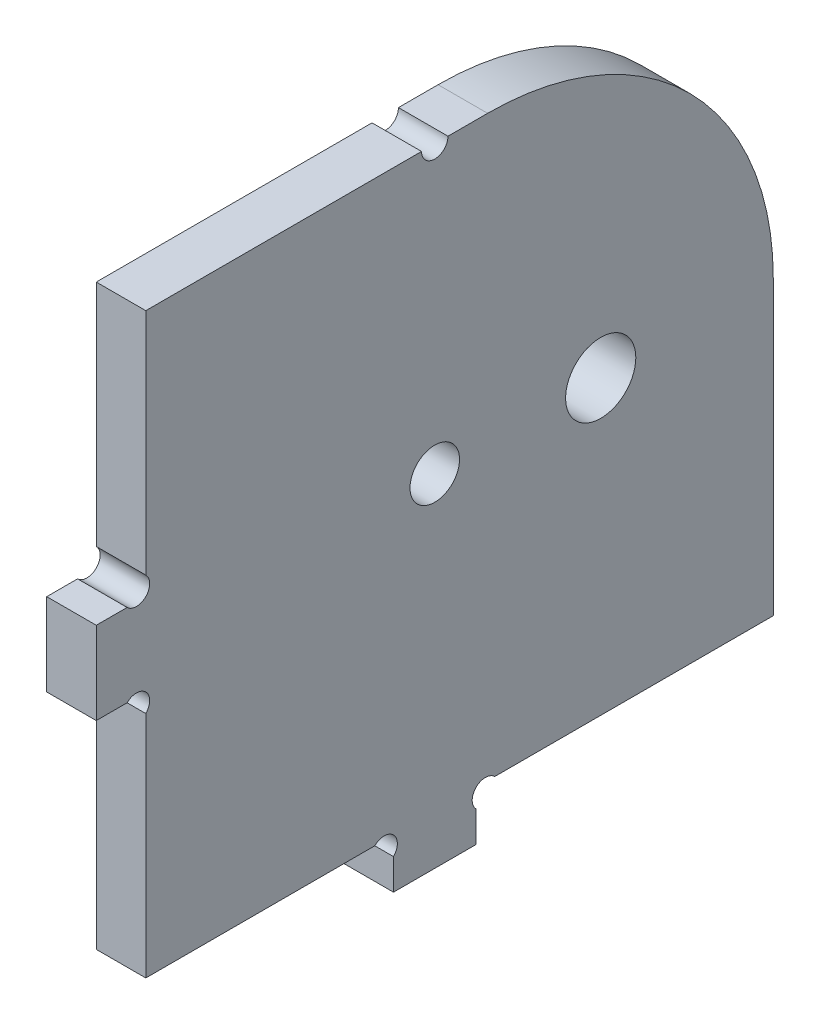
SolidWorks part; units mm, degrees
ref_plane "Plan de face" through (0, 0, 0) normal (0, 0, 1) x (1, 0, 0)
ref_plane "Plan de dessus" through (0, 0, 0) normal (0, 1, 0) x (1, 0, 0)
ref_plane "Plan de droite" through (0, 0, 0) normal (1, 0, 0) x (0, 0, -1)
sketch "Esquisse1" plane through (0, 0, 0) normal (1, 0, 0) x (0, 0, -1)
  line L0 (0, -4.5625) -> (0, 134.1836) construction
  line L1 (-32.3115, 0) -> (104.4265, 0) construction
  line L2 (-24.3695, 6) -> (94.833, 6) construction
  line L3 (6, -26.2376) -> (6, 112.02) construction
  line L4 (82, -26.2376) -> (82, 134.1836) construction
  line L5 (-26.3115, 76) -> (110.4265, 76) construction
  line L6 (41, 99.8569) -> (41, -16.9546) construction
  line L7 (94.833, 41.4) -> (32.7277, 41.4) construction
  line L8 (46, 9.2963) -> (46, -16.9546) construction
  line L9 (-8.4142, 41) -> (14.8973, 41) construction
  line L10 (-8.4142, 36) -> (14.8973, 36) construction
  line L11 (6, 36) -> (-7.6399, 22.3601) construction
  line L12 (46, 3.7373) -> (46, 0)
  line L13 (46, 6) -> (62.0517, -10.0517) construction
  line L14 (46, 0) -> (36, 0)
  line L15 (36, 0) -> (36, 3.7373)
  line L16 (3.7373, 36) -> (0, 36)
  line L17 (0, 36) -> (0, 46)
  line L18 (0, 46) -> (3.7373, 46)
  line L19 (33.7373, 6) -> (6, 6)
  line L20 (6, 6) -> (6, 33.7373)
  line L21 (6, 48.2627) -> (6, 76)
  line L22 (6, 76) -> (39.4, 76)
  line L23 (82, 41.4) -> (82, 6)
  line L24 (82, 6) -> (48.2627, 6)
  line L25 (47.4, 89.1717) -> (47.4, 36) construction
  line L26 (28, 81.2404) -> (28, 1.9905) construction
  line L27 (87.1681, 38) -> (18.3306, 38) construction
  line L28 (42.6, 76) -> (47.4, 76)
  circle A0 centre (41, 41.4) radius 3
  arc A1 (48.2627, 6) -> (46, 3.7373) centre (47.1314, 4.8686) ccw
  arc A2 (33.7373, 6) -> (36, 3.7373) centre (34.8686, 4.8686) cw
  arc A3 (6, 33.7373) -> (3.7373, 36) centre (4.8686, 34.8686) ccw
  arc A4 (6, 48.2627) -> (3.7373, 46) centre (4.8686, 47.1314) cw
  circle A5 centre (61.1, 41.4) radius 15.1 construction
  arc A6 (82, 41.4) -> (47.4, 76) centre (47.4, 41.4) ccw
  circle A7 centre (61.1, 41.4) radius 4.25
  arc A8 (39.4, 76) -> (42.6, 76) centre (41, 76) ccw
  circle A9 centre (41, 41.4) radius 5 construction
  dimension "D7" = 35
  dimension "D12" = 34.6
  dimension "D13" = 22
  dimension "D15" = 32
  dimension "D1" = 6
  dimension "D2" = 6
  dimension "D4" = 76
  dimension "D5" = 41
  dimension "D6" = 35.4
  dimension "D8" = 5
  dimension "D9" = 45
  dimension "D10" = 5
  dimension "D11" = 45
extrude "Boss.-Extru.1" add sketch "Esquisse1" along normal blind 6
